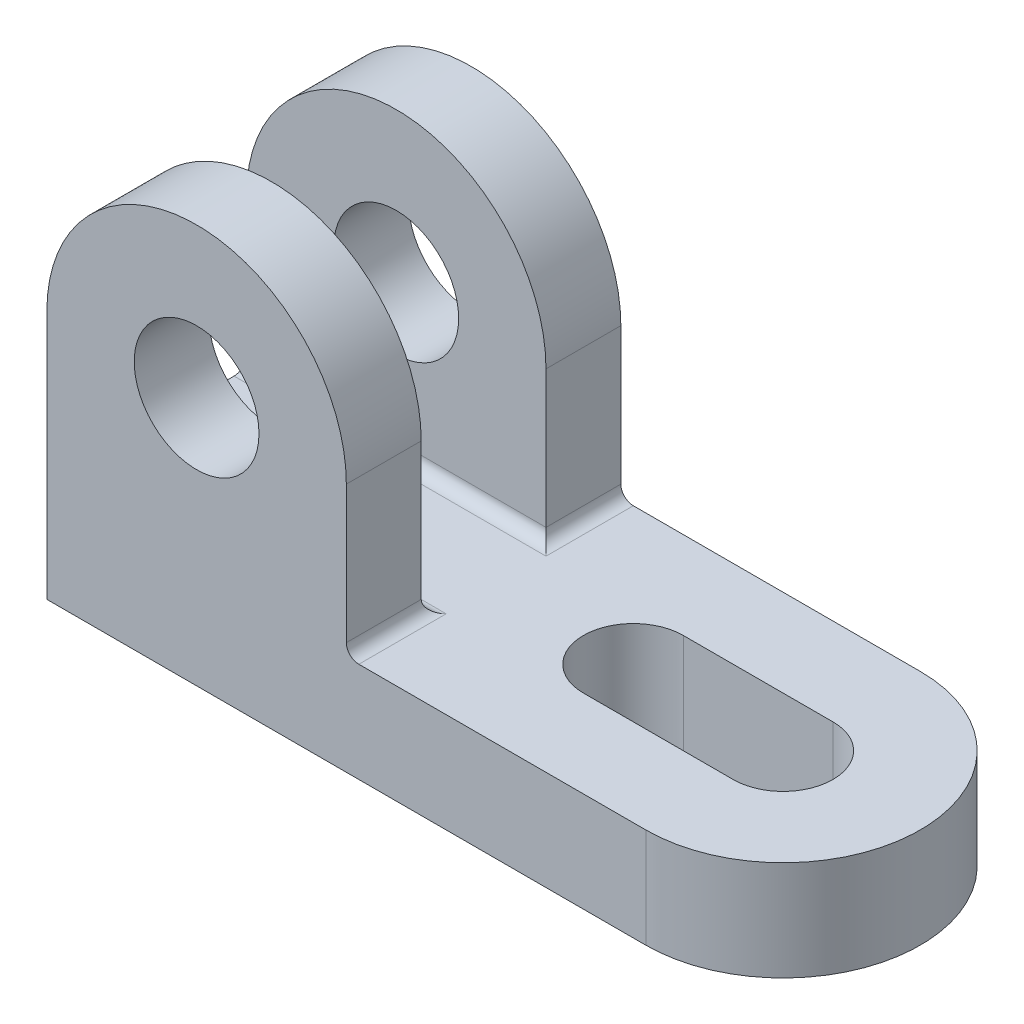
SolidWorks part; units mm, degrees
ref_plane "Front Plane" through (0, 0, 0) normal (0, 0, 1) x (1, 0, 0)
ref_plane "Top Plane" through (0, 0, 0) normal (0, 1, 0) x (1, 0, 0)
ref_plane "Right Plane" through (0, 0, 0) normal (1, 0, 0) x (0, 0, -1)
sketch "Sketch1" plane through (0, 0, 0) normal (0, 1, 0) x (1, 0, 0)
  line L0 (96, 22) -> (72, 22) construction
  line L1 (0, 0) -> (96, 0)
  line L2 (0, 0) -> (0, 44)
  line L3 (0, 44) -> (96, 44)
  line L5 (96, 22) -> (72, 22) construction
  line L6 (96, 14) -> (72, 14)
  line L7 (96, 30) -> (72, 30)
  line L8 (96, 0) -> (96, 44) construction
  arc A0 (96, 14) -> (96, 30) centre (96, 22) ccw
  arc A1 (72, 30) -> (72, 14) centre (72, 22) ccw
  arc A2 (96, 0) -> (96, 44) centre (96, 22) ccw
  point P5 (84, 22)
  dimension "D3" = 8
  dimension "D4" = 24
  dimension "D6" = 22
extrude "Boss-Extrude2" add sketch "Sketch1" along normal blind 16 contours L1 A2 L3 L2 | L7 A1 L6 A0
sketch "Sketch2" plane through (0, 0, 0) normal (0, 0, 1) x (1, 0, 0)
  line L0 (24, 40) -> (24, 16) construction
  line L1 (0, 16) -> (48, 16)
  line L2 (0, 16) -> (0, 40)
  line L4 (48, 16) -> (48, 40)
  arc A0 (48, 40) -> (0, 40) centre (24, 40) ccw
  circle A1 centre (24, 40) radius 10
  dimension "D3" = 20
  dimension "D1" = 48
  dimension "D2" = 24
extrude "Boss-Extrude3" add sketch "Sketch2" against normal blind 44
sketch "Sketch4" plane through (48, 0, 0) normal (1, 0, 0) x (0, 0, -1)
  line L0 (44, 16) -> (0, 16) construction
  line L1 (32, 16) -> (12, 16)
  line L2 (32, 16) -> (32, 64)
  line L3 (32, 64) -> (12, 64)
  line L4 (12, 16) -> (12, 64)
  line L5 (44, 64) -> (0, 64) construction
  line L6 (44, 16) -> (44, 40) construction
  dimension "D1" = 12
  dimension "D2" = 12
extrude "Cut-Extrude1" cut sketch "Sketch4" against normal through all
fillet "Fillet1" radius 2 4 edges at (48, 16, -38) (48, 16, -6) (24, 16, -32) (24, 16, -12)
